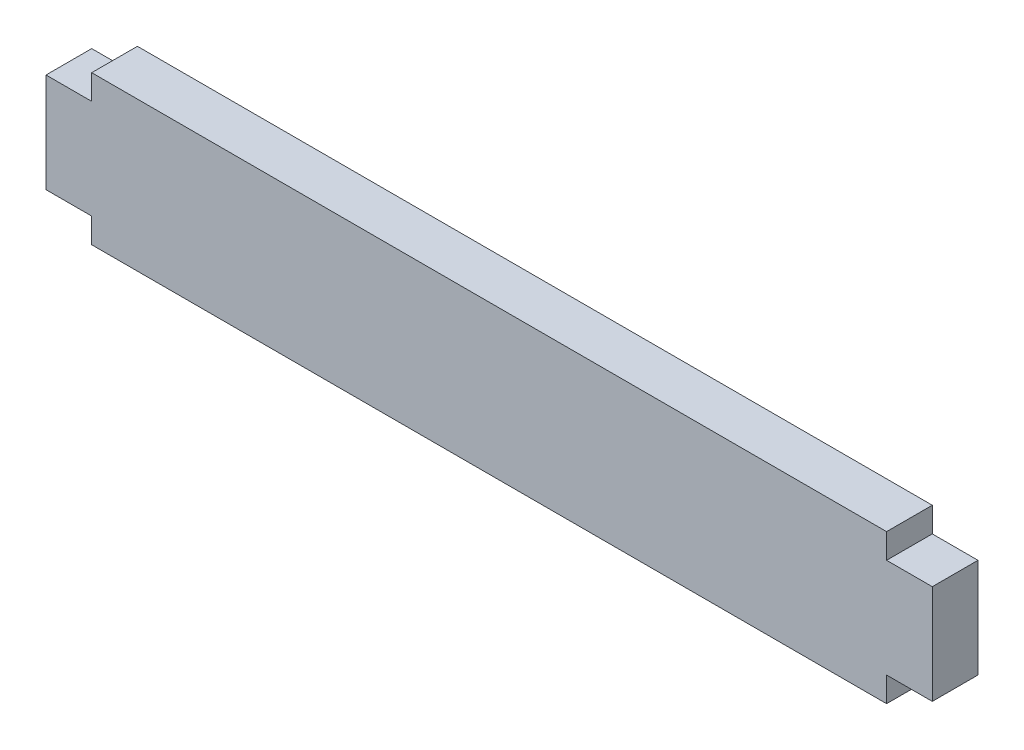
SolidWorks part; units mm, degrees
ref_plane "Front Plane" through (0, 0, 0) normal (0, 0, 1) x (1, 0, 0)
ref_plane "Top Plane" through (0, 0, 0) normal (0, 1, 0) x (1, 0, 0)
ref_plane "Right Plane" through (0, 0, 0) normal (1, 0, 0) x (0, 0, -1)
sketch "Sketch1" plane through (0, 0, 0) normal (0, 0, 1) x (1, 0, 0)
  line L0 (-50.8, 0) -> (50.8, 0) construction
  line L1 (50.8, -9.525) -> (-50.8, -9.525)
  line L2 (50.8, -9.525) -> (50.8, -6.35)
  line L3 (50.8, 9.525) -> (-50.8, 9.525)
  line L4 (-50.8, -9.525) -> (-50.8, -6.35)
  line L5 (50.8, -9.525) -> (-50.8, 9.525) construction
  line L6 (50.8, 9.525) -> (-50.8, -9.525) construction
  line L7 (-50.8, 6.35) -> (-50.8, 9.525)
  line L8 (-56.642, -6.35) -> (-50.8, -6.35)
  line L9 (-56.642, -6.35) -> (-56.642, 6.35)
  line L10 (-56.642, 6.35) -> (-50.8, 6.35)
  line L11 (0, 9.525) -> (0, -9.525) construction
  line L12 (-56.642, -6.35) -> (-50.8, 6.35) construction
  line L13 (-56.642, 6.35) -> (-50.8, -6.35) construction
  line L14 (56.642, 6.35) -> (50.8, -6.35) construction
  line L15 (56.642, -6.35) -> (50.8, 6.35) construction
  line L16 (56.642, 6.35) -> (50.8, 6.35)
  line L17 (56.642, -6.35) -> (56.642, 6.35)
  line L18 (56.642, -6.35) -> (50.8, -6.35)
  line L19 (50.8, 6.35) -> (50.8, 9.525)
  line L20 (50.8, -9.525) -> (50.8, -6.35)
  line L21 (50.8, 6.35) -> (50.8, 9.525)
  point P0 (0, 0)
  point P8 (-53.721, 0)
  point P19 (53.721, 0)
  dimension "D1" = 101.6
  dimension "D2" = 19.05
  dimension "D3" = 5.842
  dimension "D4" = 12.7
extrude "Boss-Extrude1" add sketch "Sketch1" along normal blind 5.842 contours L16 L19 L3 L7 L10 L9 L8 L4 L1 L2 L18 L17
